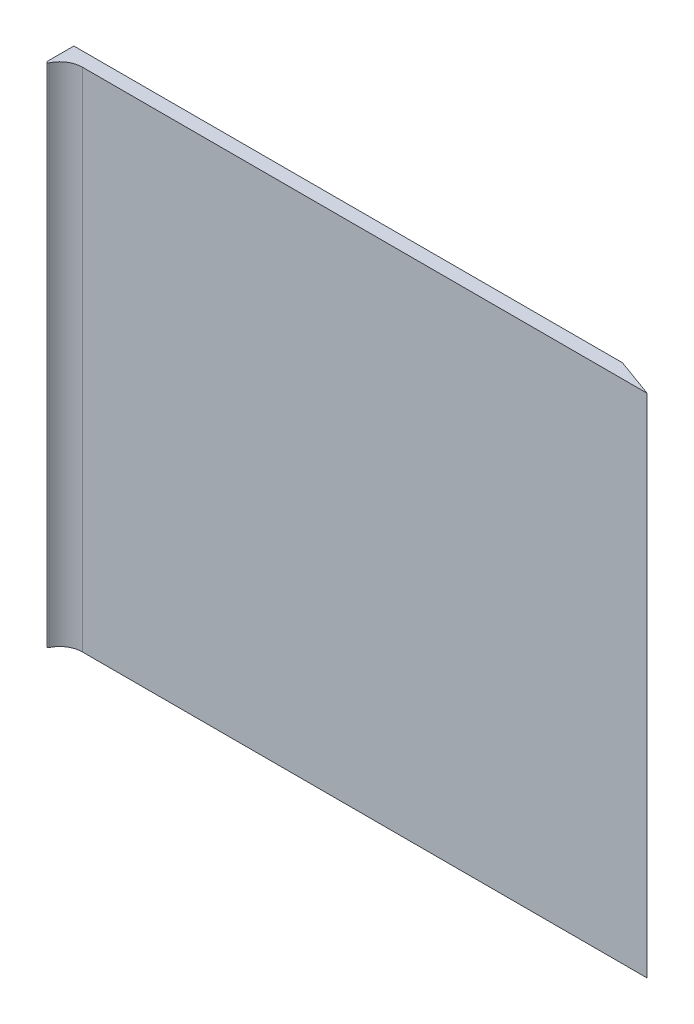
SolidWorks part; units mm, degrees
ref_plane "Front Plane" through (0, 0, 0) normal (0, 0, 1) x (1, 0, 0)
ref_plane "Top Plane" through (0, 0, 0) normal (0, 1, 0) x (1, 0, 0)
ref_plane "Right Plane" through (0, 0, 0) normal (1, 0, 0) x (0, 0, -1)
sketch "Sketch1" plane through (0, 0, 0) normal (0, 0, 1) x (1, 0, 0)
  line L0 (-97.5, 90) -> (97.5, 90)
  line L1 (-97.5, 90) -> (-97.5, -90)
  line L2 (97.5, 90) -> (97.5, -90)
  line L3 (-97.5, -90) -> (97.5, -90)
  line L4 (0, 90) -> (0, -90) construction
  point P6 (0, 0)
  dimension "D1" = 180
  dimension "D2" = 195
extrude "Boss-Extrude1" add sketch "Sketch1" along normal mid plane 5
sketch "Sketch4" plane through (0, -90, 0) normal (0, -1, 0) x (1, 0, 0)
  line L0 (-97.5, 2.5) -> (-97.5, 10.5)
  line L1 (-97.5, 2.5) -> (-89.5, 2.5)
  line L3 (-97.5, 2.5) -> (97.5, 2.5) construction
  arc A0 (-89.5, 2.5) -> (-97.5, 10.5) centre (-89.5, 10.5) cw
  point P5 (-97.5, 0.8)
  point P6 (-89.5, 0.8)
  dimension "D1" = 8
  dimension "D2" = 8
extrude "Boss-Extrude3" add sketch "Sketch4" against normal up to surface (180 mm away) up to face at (0, 90, 0)
sketch "Sketch5" plane through (0, -90, 0) normal (0, -1, 0) x (1, 0, 0)
  line L0 (97.5, 2.5) -> (97.5, -2.5)
  line L1 (97.5, -2.5) -> (111.2374, 2.5)
  line L2 (111.2374, 2.5) -> (97.5, 2.5)
  line L3 (-97.5, -2.5) -> (97.5, -2.5) construction
  dimension "D1" = 20
extrude "Boss-Extrude4" add sketch "Sketch5" against normal up to surface (180 mm away) up to face at (-18.2314, 90, 1.7686)
fillet "Fillet1" radius 0.4 1 edges at (-97.5, 0, 10.5)
